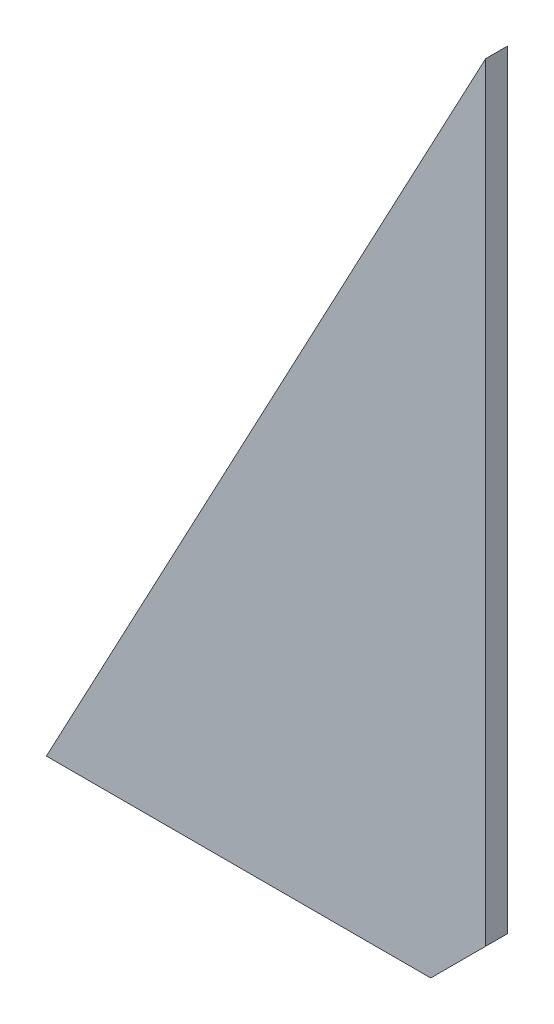
SolidWorks part; units mm, degrees
ref_plane "Plan de face" through (0, 0, 0) normal (0, 0, 1) x (1, 0, 0)
ref_plane "Plan de dessus" through (0, 0, 0) normal (0, 1, 0) x (1, 0, 0)
ref_plane "Plan de droite" through (0, 0, 0) normal (1, 0, 0) x (0, 0, -1)
sketch "Esquisse1" plane through (0, 0, 0) normal (0, 0, 1) x (1, 0, 0)
  line L0 (0, 0) -> (70, 0)
  line L1 (80, 10) -> (80, 150)
  line L2 (80, 150) -> (0, 0)
  line L3 (70, 0) -> (80, 10)
  point P1 (80, 0)
extrude "Boss.-Extru.1" add sketch "Esquisse1" along normal mid plane 4
